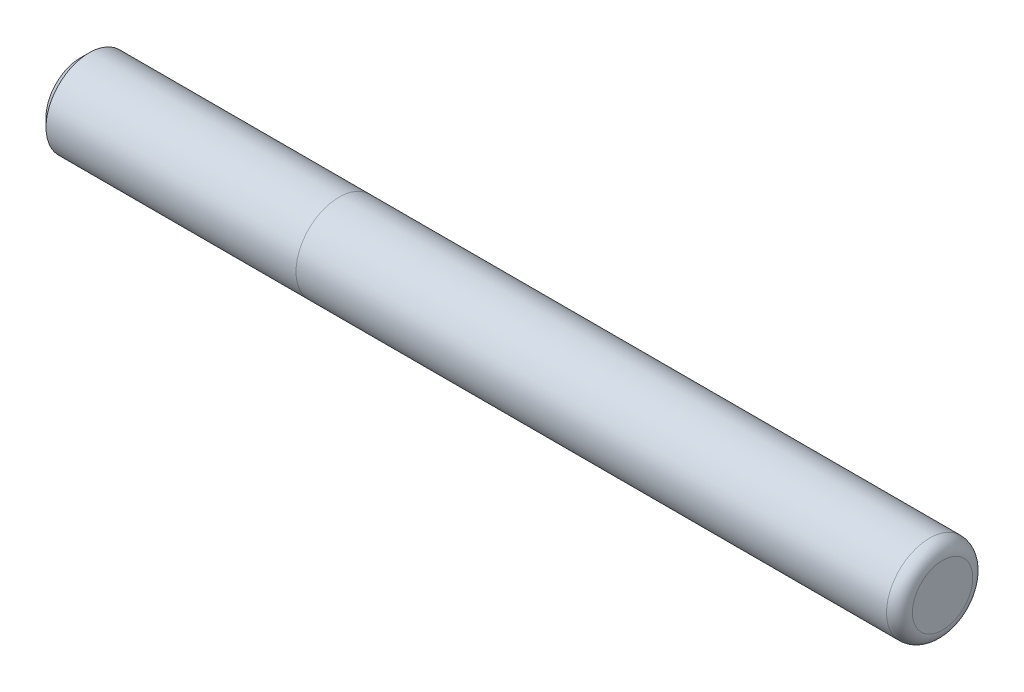
SolidWorks part; units mm, degrees
material "Stub"
ref_plane "Face" through (0, 0, 0) normal (0, 0, 1) x (1, 0, 0)
ref_plane "Dessus" through (0, 0, 0) normal (0, 1, 0) x (1, 0, 0)
ref_plane "Droite" through (0, 0, 0) normal (1, 0, 0) x (0, 0, -1)
sketch "Esquisse1" plane through (0, 0, 0) normal (0, 0, 1) x (1, 0, 0)
  line L0 (0, 0) -> (0, 3.5)
  line L1 (-1.5, 5) -> (-70, 5)
  line L2 (-70, 5) -> (-70, 4.999)
  line L3 (-70, 4.999) -> (-99, 4.999)
  line L4 (-100, 3.999) -> (-100, 0)
  line L5 (-100, 0) -> (0, 0)
  line L6 (0, 0) -> (-0.0066, -0.0902)
  line L7 (-99, 4.999) -> (-100, 3.999)
  arc A0 (0, 3.5) -> (-1.5, 5) centre (-1.5, 3.5) ccw
  point P6 (-100, 4.999)
  point P10 (0, 5)
  dimension "D5" = 1.5
  dimension "D1" = 70
  dimension "D2" = 5
  dimension "D3" = 4.999
  dimension "D4" = 30
revolve "Révolution1" add sketch "Esquisse1" angle 360 about L5
cosmetic thread "Représentation de filetage1" parameters "D2"=6.619
